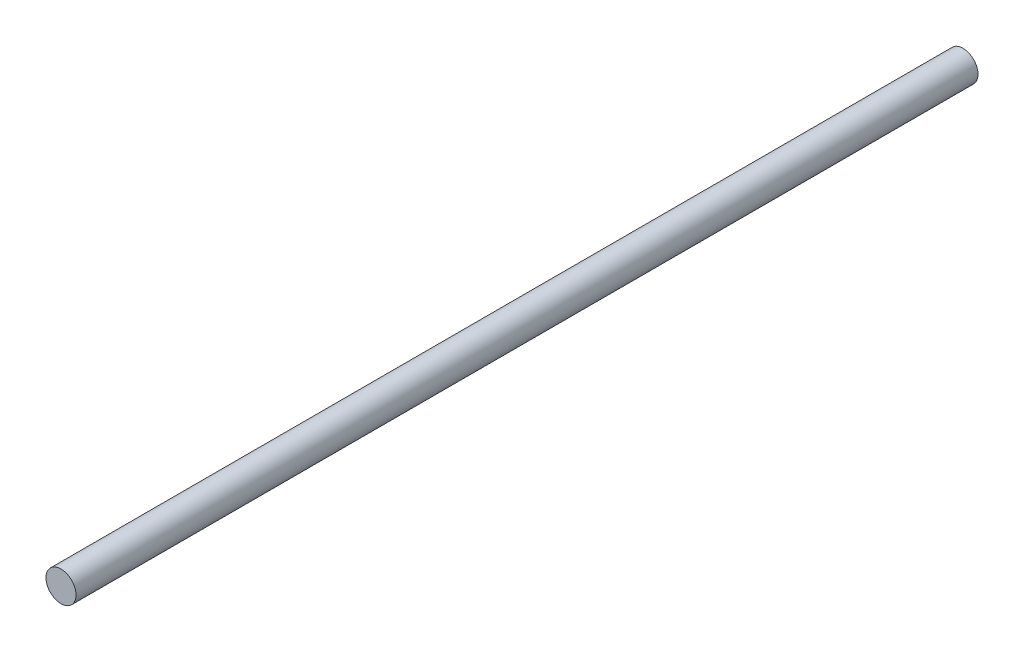
SolidWorks part; units mm, degrees
ref_plane "Front Plane" through (0, 0, 0) normal (0, 0, 1) x (1, 0, 0)
ref_plane "Top Plane" through (0, 0, 0) normal (0, 1, 0) x (1, 0, 0)
ref_plane "Right Plane" through (0, 0, 0) normal (1, 0, 0) x (0, 0, -1)
sketch "Sketch1" plane through (0, 0, 0) normal (0, 0, 1) x (1, 0, 0)
  circle A0 centre (2.8549, 19.4745) radius 2.5
  dimension "D1" = 5
extrude "Boss-Extrude2" add sketch "Sketch1" along normal blind 150
